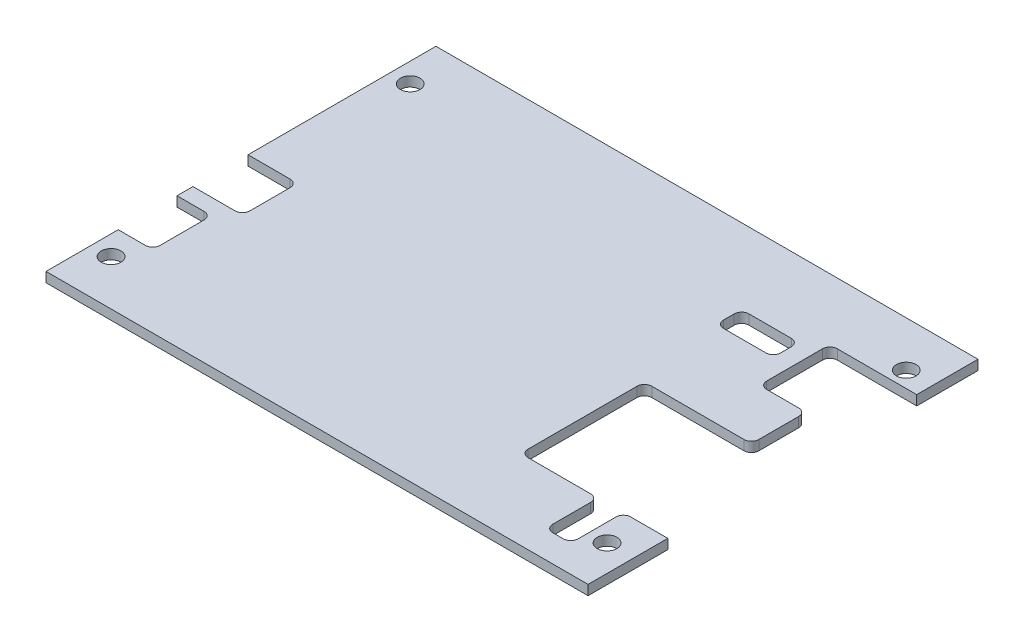
SolidWorks part; units mm, degrees
ref_plane "Front Plane" through (0, 0, 0) normal (0, 0, 1) x (1, 0, 0)
ref_plane "Top Plane" through (0, 0, 0) normal (0, 1, 0) x (1, 0, 0)
ref_plane "Right Plane" through (0, 0, 0) normal (1, 0, 0) x (0, 0, -1)
sketch "Sketch1" plane through (0, 0, 0) normal (0, 1, 0) x (1, 0, 0)
  line L0 (96.8679, 16.1009) -> (90.8948, 16.1009)
  line L1 (9.4284, 3.2405) -> (96.8679, 3.2405)
  line L2 (9.4284, 24.3752) -> (9.4284, 26.9478)
  line L3 (9.4284, 66.1405) -> (96.8679, 66.1405)
  line L4 (96.8679, 3.2405) -> (96.8679, 16.1009)
  line L5 (73.1348, 17.2915) -> (73.1348, 34.8683)
  line L6 (74.3254, 36.059) -> (89.2101, 36.059)
  line L7 (90.4007, 37.2496) -> (90.4007, 43.6842)
  line L8 (89.2101, 44.8748) -> (84.0554, 44.8748)
  line L9 (82.8648, 46.0654) -> (82.8648, 55.0654)
  line L10 (84.0554, 56.2561) -> (96.8679, 56.2561)
  line L11 (96.8679, 56.2561) -> (96.8679, 66.1405)
  line L12 (74.3254, 17.2915) -> (98.4554, 17.2915) construction
  line L13 (74.3254, 34.8683) -> (74.3254, 17.2915) construction
  line L14 (74.3254, 34.8683) -> (98.4554, 34.8683) construction
  line L15 (91.5913, 38.2488) -> (91.5913, 38.9416) construction
  line L16 (94.9554, 46.0654) -> (84.9554, 46.0654) construction
  line L17 (84.0554, 46.0654) -> (84.0554, 49.0654) construction
  line L18 (84.9554, 55.0654) -> (94.9554, 55.0654) construction
  line L19 (9.4284, 3.2405) -> (9.4284, 14.8909)
  line L20 (88.5135, 7.6078) -> (86.8073, 7.6078)
  line L21 (89.7042, 8.7984) -> (89.7042, 14.9103)
  line L22 (8.8023, 16.0815) -> (13.5023, 16.0815) construction
  line L23 (85.6167, 8.7984) -> (85.6167, 14.9103)
  line L24 (78.8815, 49.9188) -> (72.0553, 49.9188)
  line L25 (80.0722, 51.1094) -> (80.0722, 52.8157)
  line L26 (78.8815, 54.0063) -> (72.0553, 54.0063)
  line L27 (70.8647, 51.1094) -> (70.8647, 52.8157)
  line L28 (79.0284, 53.2125) -> (77.0384, 53.2125) construction
  line L29 (79.2784, 52.7125) -> (79.2784, 51.2125) construction
  line L30 (77.0384, 50.7125) -> (79.0284, 50.7125) construction
  line L31 (71.6584, 51.2125) -> (71.6584, 52.7125) construction
  line L32 (88.9104, 8.6515) -> (88.9104, 10.6415) construction
  line L33 (9.4284, 2.9905) -> (9.4284, 66.3905) construction
  line L34 (86.4104, 10.6415) -> (86.4104, 8.6515) construction
  line L35 (88.4104, 8.4015) -> (86.9104, 8.4015) construction
  line L36 (9.4284, 35.8291) -> (9.4284, 66.1405)
  line L37 (84.426, 16.1009) -> (74.3254, 16.1009)
  line L38 (16.2261, 26.9478) -> (9.4284, 26.9478)
  line L39 (17.4167, 28.1385) -> (17.4167, 34.6385)
  line L40 (16.2261, 35.8291) -> (9.4284, 35.8291)
  line L41 (96.8679, 68.3905) -> (96.8679, 66.3905) construction
  line L42 (13.8023, 14.8909) -> (9.4284, 14.8909)
  line L43 (14.9929, 16.0815) -> (14.9929, 23.1846)
  line L44 (13.8023, 24.3752) -> (9.4284, 24.3752)
  line L45 (53.1482, 3.2405) -> (53.1482, 66.1405) construction
  line L46 (22.1181, 33.1287) -> (96.8679, 33.1287) construction
  line L47 (12.6034, 58.8205) -> (12.6034, 66.1405) construction
  line L48 (13.8023, 16.8315) -> (13.8023, 17.3815) construction
  line L49 (13.5023, 23.5815) -> (8.8023, 23.5815) construction
  line L50 (8.7261, 28.1385) -> (16.2261, 28.1385) construction
  line L51 (16.2261, 28.5885) -> (16.2261, 29.4965) construction
  line L53 (16.2261, 34.6385) -> (8.7261, 34.6385) construction
  line L55 (12.6034, 10.5605) -> (12.6034, 3.2405) construction
  circle A0 centre (92.6134, 58.8205) radius 1.5875
  circle A1 centre (12.6034, 10.5605) radius 1.5875
  circle A2 centre (92.6134, 10.5605) radius 1.5875
  circle A3 centre (12.6034, 58.8205) radius 1.5875
  arc A4 (17.4167, 34.6385) -> (16.2261, 35.8291) centre (16.2261, 34.6385) ccw
  arc A5 (16.2261, 26.9478) -> (17.4167, 28.1385) centre (16.2261, 28.1385) ccw
  arc A6 (14.9929, 23.1846) -> (13.8023, 24.3752) centre (13.8023, 23.1846) ccw
  arc A7 (13.8023, 14.8909) -> (14.9929, 16.0815) centre (13.8023, 16.0815) ccw
  arc A8 (72.0553, 49.9188) -> (70.8647, 51.1094) centre (72.0553, 51.1094) cw
  arc A9 (72.0553, 54.0063) -> (70.8647, 52.8157) centre (72.0553, 52.8157) ccw
  arc A10 (80.0722, 52.8157) -> (78.8815, 54.0063) centre (78.8815, 52.8157) ccw
  arc A11 (78.8815, 49.9188) -> (80.0722, 51.1094) centre (78.8815, 51.1094) ccw
  arc A12 (82.8648, 55.0654) -> (84.0554, 56.2561) centre (84.0554, 55.0654) cw
  arc A13 (84.0554, 44.8748) -> (82.8648, 46.0654) centre (84.0554, 46.0654) cw
  arc A14 (90.4007, 43.6842) -> (89.2101, 44.8748) centre (89.2101, 43.6842) ccw
  arc A15 (89.2101, 36.059) -> (90.4007, 37.2496) centre (89.2101, 37.2496) ccw
  arc A16 (90.8948, 16.1009) -> (89.7042, 14.9103) centre (90.8948, 14.9103) ccw
  arc A17 (84.426, 16.1009) -> (85.6167, 14.9103) centre (84.426, 14.9103) cw
  arc A18 (86.8073, 7.6078) -> (85.6167, 8.7984) centre (86.8073, 8.7984) cw
  arc A19 (88.5135, 7.6078) -> (89.7042, 8.7984) centre (88.5135, 8.7984) ccw
  arc A20 (73.1348, 34.8683) -> (74.3254, 36.059) centre (74.3254, 34.8683) cw
  arc A21 (74.3254, 16.1009) -> (73.1348, 17.2915) centre (74.3254, 17.2915) cw
  dimension "D10" = 3.175
  dimension "D26" = 1.1906
  dimension "D27" = 1.1906
  dimension "D28" = 1.1906
  dimension "D29" = 1.1906
  dimension "D30" = 1.1906
  dimension "D31" = 1.1906
  dimension "D32" = 1.1906
  dimension "D33" = 1.1906
  dimension "D34" = 1.1906
  dimension "D35" = 1.1906
  dimension "D36" = 1.1906
  dimension "D37" = 1.1906
  dimension "D38" = 1.1906
  dimension "D39" = 1.1906
  dimension "D40" = 1.1906
  dimension "D41" = 1.1906
  dimension "D42" = 1.1906
  dimension "D43" = 1.1906
  dimension "D1" = 62.9
  dimension "D3" = 1.1906
  dimension "D4" = 1.1906
  dimension "D5" = 1.1906
  dimension "D6" = 1.1906
  dimension "D7" = 1.1906
  dimension "D8" = 1.1906
  dimension "D9" = 1.1906
  dimension "D11" = 0.7937
  dimension "D12" = 0.7937
  dimension "D13" = 0.7937
  dimension "D14" = 0.7937
  dimension "D15" = 0.7937
  dimension "D16" = 0.7937
  dimension "D17" = 0.7937
  dimension "D18" = 1.1906
  dimension "D19" = 25.5209
  dimension "D20" = 1.1906
  dimension "D21" = 0.7937
  dimension "D22" = 1.1906
  dimension "D23" = 1.1906
  dimension "D25" = 1.1906
extrude "Boss-Extrude1" add sketch "Sketch1" along normal blind 1.5875
